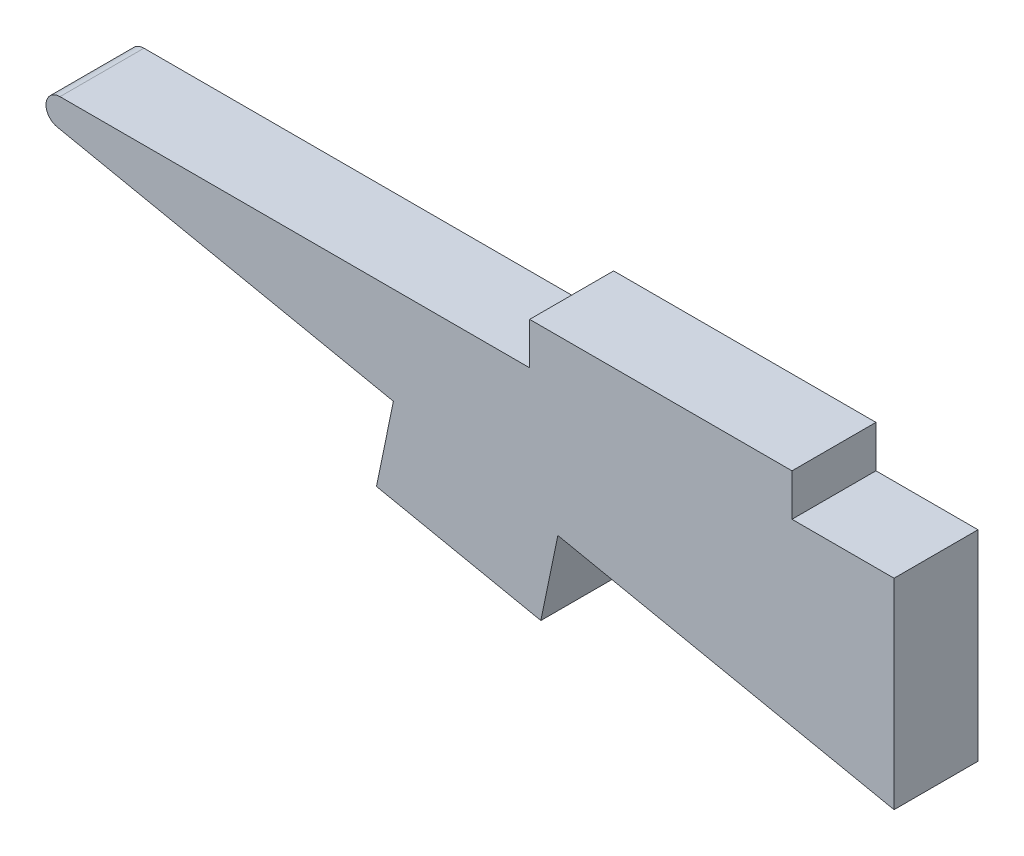
SolidWorks part; units mm, degrees
ref_plane "Front Plane" through (0, 0, 0) normal (0, 0, 1) x (1, 0, 0)
ref_plane "Top Plane" through (0, 0, 0) normal (0, 1, 0) x (1, 0, 0)
ref_plane "Right Plane" through (0, 0, 0) normal (1, 0, 0) x (0, 0, -1)
sketch "Sketch1" plane through (0, 0, 0) normal (0, 0, 1) x (1, 0, 0)
  line L0 (-6.2865, -0.762) -> (-6.2865, -1.524)
  line L2 (-6.2865, -1.524) -> (-4.4335, -1.524)
  line L3 (-4.4335, -1.524) -> (-4.4335, -5.164)
  line L4 (-11.049, -0.762) -> (-11.049, -1.524)
  line L6 (-11.049, -1.524) -> (-22.0622, -1.524)
  line L7 (-22.0622, -1.524) -> (-13.5225, -3.2873)
  line L8 (-11.049, -0.762) -> (-6.2865, -0.762)
  line L10 (-13.5225, -3.2873) -> (-13.8307, -4.7798)
  line L11 (-10.5375, -3.9036) -> (-10.8457, -5.3962)
  line L13 (-13.8307, -4.7798) -> (-10.8457, -5.3962)
  line L14 (-10.5375, -3.9036) -> (-4.4335, -5.164)
extrude "Boss-Extrude1" add sketch "Sketch1" along normal blind 1.524
fillet "Fillet1" radius 0.254 1 edges at (-22.0622, -1.524, 0.762)
